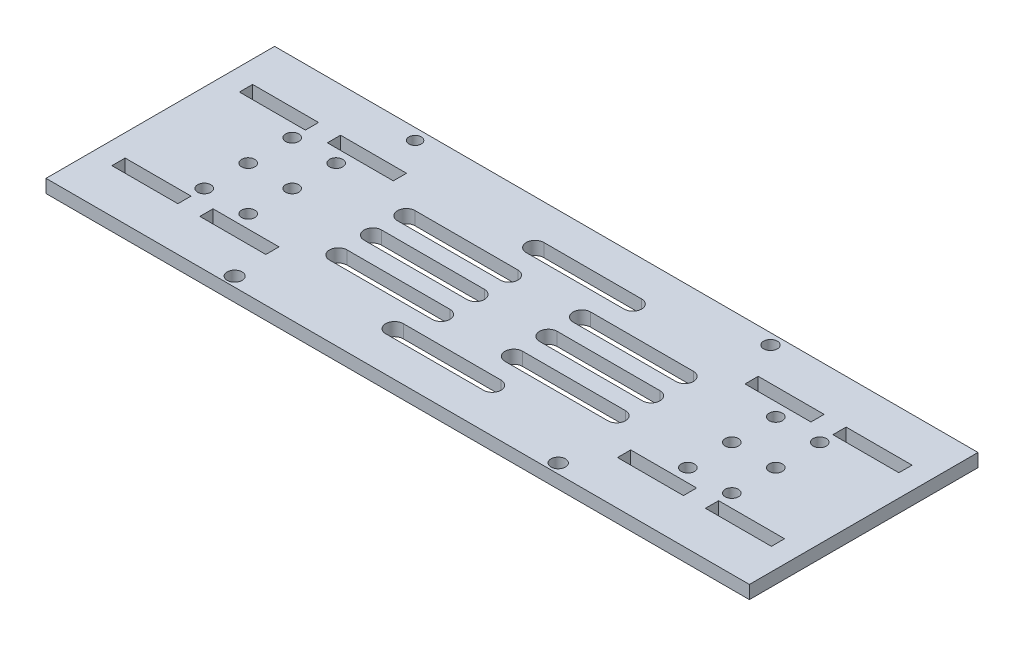
SolidWorks part; units mm, degrees
ref_plane "Front Plane" through (0, 0, 0) normal (0, 0, 1) x (1, 0, 0)
ref_plane "Top Plane" through (0, 0, 0) normal (0, 1, 0) x (1, 0, 0)
ref_plane "Right Plane" through (0, 0, 0) normal (1, 0, 0) x (0, 0, -1)
sketch "Sketch1" plane through (0, 0, 0) normal (0, 1, 0) x (1, 0, 0)
  line L0 (0, 0) -> (-15.3333, 0) construction
  line L1 (80, 26) -> (-80, 26)
  line L2 (80, 26) -> (80, -26)
  line L3 (80, -26) -> (-80, -26)
  line L4 (-80, 26) -> (-80, -26)
  line L5 (0, 26) -> (0, -26) construction
  line L6 (75, 16) -> (60, 16)
  line L7 (75, 16) -> (75, 13)
  line L8 (75, 13) -> (60, 13)
  line L9 (60, 16) -> (60, 13)
  line L10 (55, 16) -> (40, 16)
  line L11 (55, 16) -> (55, 13)
  line L12 (55, 13) -> (40, 13)
  line L13 (40, 16) -> (40, 13)
  line L15 (0, 0) -> (0, -4.375) construction
  line L19 (60, -16) -> (60, -13)
  line L20 (75, -13) -> (60, -13)
  line L21 (75, -16) -> (75, -13)
  line L22 (75, -16) -> (60, -16)
  line L23 (40, -16) -> (40, -13)
  line L24 (55, -13) -> (40, -13)
  line L25 (55, -16) -> (55, -13)
  line L26 (55, -16) -> (40, -16)
  line L28 (-55, -16) -> (-40, -16)
  line L29 (-55, -16) -> (-55, -13)
  line L30 (-55, -13) -> (-40, -13)
  line L31 (-40, -16) -> (-40, -13)
  line L32 (-75, -16) -> (-60, -16)
  line L33 (-75, -16) -> (-75, -13)
  line L34 (-75, -13) -> (-60, -13)
  line L35 (-60, -16) -> (-60, -13)
  line L40 (-40, 16) -> (-40, 13)
  line L41 (-55, 13) -> (-40, 13)
  line L42 (-55, 16) -> (-55, 13)
  line L43 (-55, 16) -> (-40, 16)
  line L44 (-60, 16) -> (-60, 13)
  line L45 (-75, 13) -> (-60, 13)
  line L46 (-75, 16) -> (-75, 13)
  line L47 (-75, 16) -> (-60, 16)
  circle A0 centre (50, 10) radius 1.5
  circle A1 centre (60, 10) radius 1.5
  circle A2 centre (60, 0) radius 1.5
  circle A3 centre (50, 0) radius 1.5
  circle A4 centre (50, -10) radius 1.5
  circle A5 centre (60, -10) radius 1.5
  circle A6 centre (-60, -10) radius 1.5
  circle A7 centre (-50, -10) radius 1.5
  circle A8 centre (-50, 0) radius 1.5
  circle A9 centre (-60, 0) radius 1.5
  circle A10 centre (-60, 10) radius 1.5
  circle A11 centre (-50, 10) radius 1.5
  dimension "D1" = 3
  dimension "D2" = 15
  dimension "D3" = 5
  dimension "D4" = 5
  dimension "D5" = 15
  dimension "D6" = 13
  dimension "D7" = 52
  dimension "D8" = 26
  dimension "D11" = 80
extrude "Boss-Extrude1" add sketch "Sketch1" along normal blind 3
sketch "Sketch2" plane through (0, 3, 0) normal (0, 1, 0) x (1, 0, 0)
  line L0 (-31.6585, 2) -> (-8.2664, 2)
  line L1 (31.6585, -9.8567) -> (8.2664, -9.8567)
  line L2 (31.6585, -5.8567) -> (8.2664, -5.8567)
  line L3 (-10.7477, 17.9876) -> (11.4995, 17.9876)
  line L4 (-31.6585, -2) -> (-8.2664, -2)
  line L5 (-31.6585, 9.6208) -> (-8.2664, 9.6208)
  line L6 (-31.6585, 5.6208) -> (-8.2664, 5.6208)
  line L7 (31.6585, 5.6208) -> (8.2664, 5.6208)
  line L8 (31.6585, 9.6208) -> (8.2664, 9.6208)
  line L9 (-31.6585, -5.8567) -> (-8.2664, -5.8567)
  line L10 (31.6585, -2) -> (8.2664, -2)
  line L11 (31.6585, 2) -> (8.2664, 2)
  line L12 (-31.6585, -9.8567) -> (-8.2664, -9.8567)
  line L13 (-10.7477, -13.9876) -> (11.4995, -13.9876)
  line L14 (-10.7477, -17.9876) -> (11.4995, -17.9876)
  line L15 (0, 0) -> (-4.1634, 0) construction
  line L16 (-10.7477, 13.9876) -> (11.4995, 13.9876)
  arc A0 (31.6585, -9.8567) -> (31.6585, -5.8567) centre (31.6585, -7.8567) ccw
  arc A1 (8.2664, -5.8567) -> (8.2664, -9.8567) centre (8.2664, -7.8567) ccw
  arc A2 (-8.2664, 2) -> (-8.2664, -2) centre (-8.2664, 0) cw
  arc A3 (-31.6585, -2) -> (-31.6585, 2) centre (-31.6585, 0) cw
  arc A4 (31.6585, 5.6208) -> (31.6585, 9.6208) centre (31.6585, 7.6208) ccw
  arc A5 (8.2664, 9.6208) -> (8.2664, 5.6208) centre (8.2664, 7.6208) ccw
  arc A6 (31.6585, -2) -> (31.6585, 2) centre (31.6585, 0) ccw
  arc A7 (8.2664, 2) -> (8.2664, -2) centre (8.2664, 0) ccw
  arc A8 (-8.2664, 9.6208) -> (-8.2664, 5.6208) centre (-8.2664, 7.6208) cw
  arc A9 (-31.6585, 5.6208) -> (-31.6585, 9.6208) centre (-31.6585, 7.6208) cw
  arc A10 (-8.2664, -5.8567) -> (-8.2664, -9.8567) centre (-8.2664, -7.8567) cw
  arc A11 (-31.6585, -9.8567) -> (-31.6585, -5.8567) centre (-31.6585, -7.8567) cw
  arc A12 (-10.7477, -13.9876) -> (-10.7477, -17.9876) centre (-10.7477, -15.9876) ccw
  arc A13 (11.4995, -17.9876) -> (11.4995, -13.9876) centre (11.4995, -15.9876) ccw
  arc A14 (11.4995, 17.9876) -> (11.4995, 13.9876) centre (11.4995, 15.9876) cw
  arc A15 (-10.7477, 13.9876) -> (-10.7477, 17.9876) centre (-10.7477, 15.9876) cw
  dimension "D1" = 4
extrude "Cut-Extrude1" cut sketch "Sketch2" against normal blind 3
sketch "Sketch3" plane through (0, 3, 0) normal (0, 1, 0) x (1, 0, 0)
  circle A0 centre (34.3231, -23.8155) radius 1.6358
  circle A1 centre (-39.2763, -23.8155) radius 1.6925
  circle A2 centre (-45.4844, 23.4378) radius 1.4101
  circle A3 centre (35.2358, 23.5655) radius 1.5508
extrude "Cut-Extrude2" cut sketch "Sketch3" against normal blind 10
sketch "Sketch4" plane through (0, 0, 0) normal (0, -1, 0) x (1, 0, 0)
  line L4 (80, -26) -> (80, 26)
  line L5 (80, 26) -> (-80, 26)
  line L6 (-80, 26) -> (-80, -26)
  line L7 (-80, -26) -> (80, -26)
  line L8 (80, -26) -> (80, 26)
  line L9 (80, 26) -> (-80, 26)
  line L10 (-80, 26) -> (-80, -26)
  line L11 (-80, -26) -> (80, -26)
  dimension "D1" = 0
